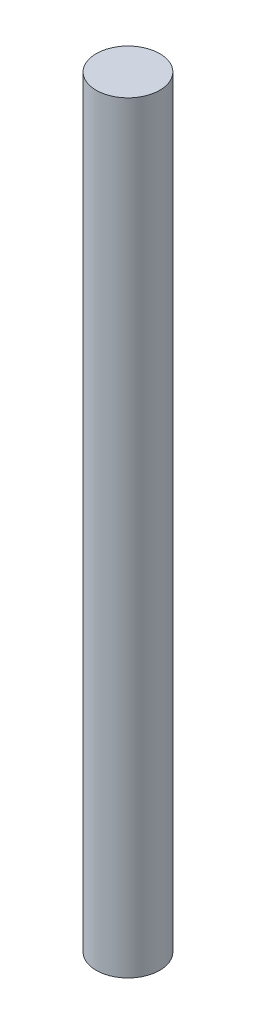
SolidWorks part; units mm, degrees
ref_plane "Front Plane" through (0, 0, 0) normal (0, 0, 1) x (1, 0, 0)
ref_plane "Top Plane" through (0, 0, 0) normal (0, 1, 0) x (1, 0, 0)
ref_plane "Right Plane" through (0, 0, 0) normal (1, 0, 0) x (0, 0, -1)
sketch "Sketch2" plane through (0, 0, 0) normal (0, 1, 0) x (1, 0, 0)
  circle A0 centre (0, 0) radius 30
  dimension "D1" = 60
extrude "Boss-Extrude1" add sketch "Sketch2" along normal blind 720
